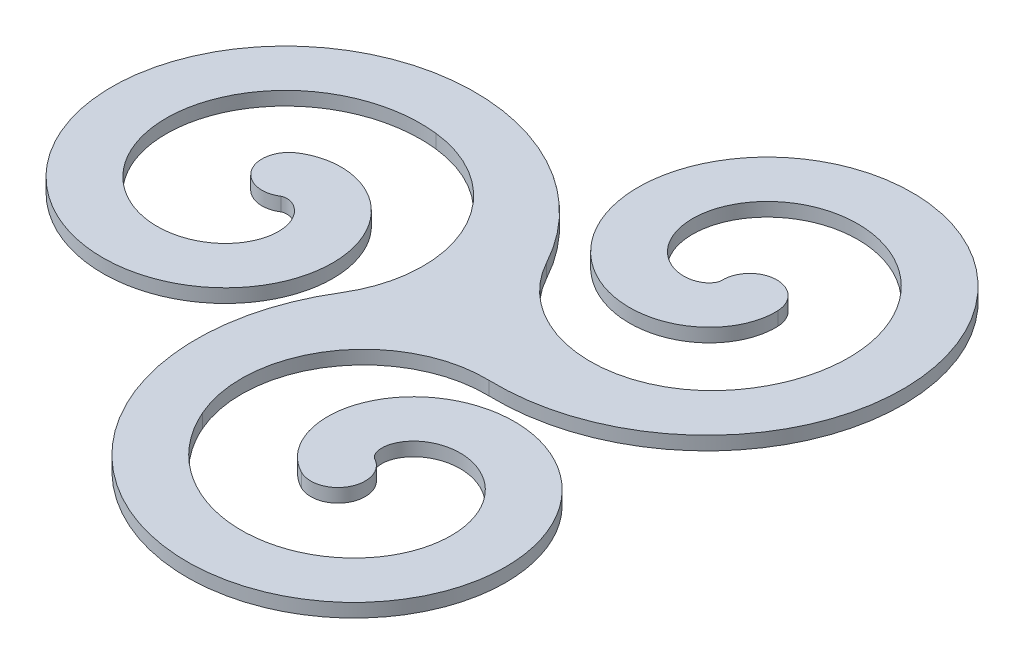
SolidWorks part; units mm, degrees
ref_plane "Ebene vorne" through (0, 0, 0) normal (0, 0, 1) x (1, 0, 0)
ref_plane "Ebene oben" through (0, 0, 0) normal (0, 1, 0) x (1, 0, 0)
ref_plane "Ebene rechts" through (0, 0, 0) normal (1, 0, 0) x (0, 0, -1)
sketch "Skizze1" plane through (0, 0, 0) normal (0, 1, 0) x (1, 0, 0)
  circle A0 centre (25, 0) radius 25
  dimension "D1" = 50
curve "Spirale/Helix1"
sketch "Skizze2" plane through (0, 0, 0) normal (0, 1, 0) x (1, 0, 0)
  arc A0 (35.7406, 8.1287) -> (14.2594, 41.8713) centre (25, 25) cw
  arc A1 (155.1116, -2.1102) -> (194.8884, 2.1102) centre (175, 0) ccw
  spline S0 degree 3 poles (908.2813, 493.7868) (28.4367, -157.1574) (-22.3322, 13.7047) (34.634, 28.7284) (37.4864, 29.0552) (43.449, 28.8209) (46.5585, 28.2594) (52.7591, 26.1542) (55.8493, 24.6101) (61.7076, 20.5299) (64.4748, 17.9937) (69.3815, 12.0105) (71.52, 8.5638) (74.8885, 0.9316) (76.1176, -3.2534) (77.4368, -12.1075) (77.5263, -16.776) (76.4101, -26.2759) (75.2039, -31.1064) (71.432, -40.5637) (68.8662, -45.1895) (62.4154, -53.8524) (58.5305, -57.8885) (49.5903, -64.9976) (44.5354, -68.0697) (33.5089, -72.9182) (27.5379, -74.6937) (15.0253, -76.6863) (8.4846, -76.9027) (-4.7487, -75.6097) (-11.4404, -74.0999) (-21.2435, -70.5012) (-24.4719, -69.0803) (-30.7904, -65.8009) (-33.8805, -63.9424) (-39.8631, -59.8013) (-42.7556, -57.5186) (-48.2845, -52.5502) (-50.9211, -49.8646) (-55.8824, -44.1198) (-58.2073, -41.0606) (-62.4928, -34.6056) (-64.4536, -31.2098) (-67.9632, -24.1258) (-69.512, -20.4376) (-72.1553, -12.8198) (-73.2498, -8.8903) (-74.9486, -0.8466) (-75.5529, 3.2674) (-76.2426, 11.6179) (-76.3279, 15.8543) (-75.959, 24.3831) (-75.5048, 28.6755) (-74.0445, 37.2467) (-73.0385, 41.5255) (-70.4717, 49.998) (-68.9109, 54.1916) (-65.2408, 62.4212) (-63.1315, 66.457) (-58.3802, 74.299) (-55.7383, 78.1049) (-49.9471, 85.4165) (-46.7978, 88.922) (-40.0268, 95.5648) (-36.4051, 98.7021) (-28.7328, 104.5448) (-24.6824, 107.2503) (-16.205, 112.1711) (-11.7781, 114.3864) (-2.6081, 118.2751) (2.135, 119.9485) (11.8702, 122.7089) (16.8622, 123.7959) (27.0217, 125.3478) (32.1892, 125.8126) (42.6214, 126.0935) (47.8859, 125.9096) (58.4299, 124.8764) (63.7093, 124.0271) (74.1979, 121.6571) (79.4072, 120.1364) (89.6696, 116.4285) (94.7227, 114.2412) (104.5868, 109.2162) (109.3979, 106.3784) (118.6938, 100.0793) (123.1785, 96.618) (131.7407, 89.11) (135.8181, 85.0633) (143.4889, 76.4329) (147.0822, 71.8494) (153.7142, 62.2041) (156.7527, 57.1423) (162.2116, 46.6087) (164.6319, 41.1367) (168.7991, 29.859) (170.546, 24.0533) (208.9501, -140.1066) (-9.8988, -387.3194) (-816.6254, 129.0757) knots -0.619464 -0.619464 -0.619464 -0.619464 0.03125 0.03125 0.0625 0.0625 0.09375 0.09375 0.125 0.125 0.15625 0.15625 0.1875 0.1875 0.21875 0.21875 0.25 0.25 0.28125 0.28125 0.3125 0.3125 0.34375 0.34375 0.375 0.375 0.40625 0.40625 0.4375 0.4375 0.46875 0.46875 0.484375 0.484375 0.5 0.5 0.515625 0.515625 0.53125 0.53125 0.546875 0.546875 0.5625 0.5625 0.578125 0.578125 0.59375 0.59375 0.609375 0.609375 0.625 0.625 0.640625 0.640625 0.65625 0.65625 0.671875 0.671875 0.6875 0.6875 0.703125 0.703125 0.71875 0.71875 0.734375 0.734375 0.75 0.75 0.765625 0.765625 0.78125 0.78125 0.796875 0.796875 0.8125 0.8125 0.828125 0.828125 0.84375 0.84375 0.859375 0.859375 0.875 0.875 0.890625 0.890625 0.90625 0.90625 0.921875 0.921875 0.9375 0.9375 0.953125 0.953125 0.96875 0.96875 0.984375 0.984375 1.401238 1.401238 1.401238 1.401238 only from (25, 25) to (175, 0) construction
  spline S1 degree 3 poles (25, 25) (27.0453, 26.3021) (29.4133, 27.3515) (34.634, 28.7284) (37.4864, 29.0552) (43.449, 28.8209) (46.5585, 28.2594) (52.7591, 26.1542) (55.8493, 24.6101) (61.7076, 20.5299) (64.4748, 17.9937) (69.3815, 12.0105) (71.52, 8.5638) (74.8885, 0.9316) (76.1176, -3.2534) (77.4368, -12.1075) (77.5263, -16.776) (76.4101, -26.2759) (75.2039, -31.1064) (71.432, -40.5637) (68.8662, -45.1895) (62.4154, -53.8524) (58.5305, -57.8885) (49.5903, -64.9976) (44.5354, -68.0697) (33.5089, -72.9182) (27.5379, -74.6937) (15.0253, -76.6863) (8.4846, -76.9027) (-4.7487, -75.6097) (-11.4404, -74.0999) (-21.2435, -70.5012) (-24.4719, -69.0803) (-30.7904, -65.8009) (-33.8805, -63.9424) (-39.8631, -59.8013) (-42.7556, -57.5186) (-48.2845, -52.5502) (-50.9211, -49.8646) (-55.8824, -44.1198) (-58.2073, -41.0606) (-62.4928, -34.6056) (-64.4536, -31.2098) (-67.9632, -24.1258) (-69.512, -20.4376) (-72.1553, -12.8198) (-73.2498, -8.8903) (-74.9486, -0.8466) (-75.5529, 3.2674) (-76.2426, 11.6179) (-76.3279, 15.8543) (-75.959, 24.3831) (-75.5048, 28.6755) (-74.0445, 37.2467) (-73.0385, 41.5255) (-70.4717, 49.998) (-68.9109, 54.1916) (-65.2408, 62.4212) (-63.1315, 66.457) (-58.3802, 74.299) (-55.7383, 78.1049) (-49.9471, 85.4165) (-46.7978, 88.922) (-40.0268, 95.5648) (-36.4051, 98.7021) (-28.7328, 104.5448) (-24.6824, 107.2503) (-16.205, 112.1711) (-11.7781, 114.3864) (-2.6081, 118.2751) (2.135, 119.9485) (11.8702, 122.7089) (16.8622, 123.7959) (27.0217, 125.3478) (32.1892, 125.8126) (42.6214, 126.0935) (47.8859, 125.9096) (58.4299, 124.8764) (63.7093, 124.0271) (74.1979, 121.6571) (79.4072, 120.1364) (89.6696, 116.4285) (94.7227, 114.2412) (104.5868, 109.2162) (109.3979, 106.3784) (118.6938, 100.0793) (123.1785, 96.618) (131.7407, 89.11) (135.8181, 85.0633) (143.4889, 76.4329) (147.0822, 71.8494) (153.7142, 62.2041) (156.7527, 57.1423) (162.2116, 46.6087) (164.6319, 41.1367) (168.7991, 29.859) (170.546, 24.0533) (173.321, 12.1917) (174.349, 6.1359) (175, 0) knots 0 0 0 0 0.03125 0.03125 0.0625 0.0625 0.09375 0.09375 0.125 0.125 0.15625 0.15625 0.1875 0.1875 0.21875 0.21875 0.25 0.25 0.28125 0.28125 0.3125 0.3125 0.34375 0.34375 0.375 0.375 0.40625 0.40625 0.4375 0.4375 0.46875 0.46875 0.484375 0.484375 0.5 0.5 0.515625 0.515625 0.53125 0.53125 0.546875 0.546875 0.5625 0.5625 0.578125 0.578125 0.59375 0.59375 0.609375 0.609375 0.625 0.625 0.640625 0.640625 0.65625 0.65625 0.671875 0.671875 0.6875 0.6875 0.703125 0.703125 0.71875 0.71875 0.734375 0.734375 0.75 0.75 0.765625 0.765625 0.78125 0.78125 0.796875 0.796875 0.8125 0.8125 0.828125 0.828125 0.84375 0.84375 0.859375 0.859375 0.875 0.875 0.890625 0.890625 0.90625 0.90625 0.921875 0.921875 0.9375 0.9375 0.953125 0.953125 0.96875 0.96875 0.984375 0.984375 1 1 1 1 construction
  spline S2 degree 1 poles (35.7406, 8.1287) (155.1116, -2.1102) knots 0 0 1 1 construction
  spline S3 degree 3 poles (35.7406, 8.1287) (35.8159, 8.1767) (35.9534, 8.2571) (36.381, 8.4663) (37.0711, 8.714) (38.216, 8.9346) (40.1146, 9.0131) (43.1288, 8.5114) (47.3461, 6.4526) (51.5749, 2.628) (55.1346, -3.0458) (57.3291, -10.4114) (57.5224, -19.0758) (55.2104, -28.4373) (50.0814, -37.7314) (42.0622, -46.0931) (31.3445, -52.6299) (18.3901, -56.5013) (3.9124, -56.9978) (-11.1634, -53.6132) (-25.7606, -46.1043) (-38.7271, -34.5327) (-48.9222, -19.2843) (-55.3072, -1.0649) (-57.0346, 19.1303) (-53.5273, 40.0705) (-44.5416, 60.365) (-30.2096, 78.5549) (-11.056, 93.2158) (12.0137, 103.0632) (37.7524, 107.0547) (64.6387, 104.4797) (90.9664, 95.0299) (114.9539, 78.8477) (131.5416, 60.2566) (141.9883, 42.8543) (148.2436, 28.7159) (152.0148, 16.1832) (154.1026, 5.827) (154.8309, 0.5361) (155.1116, -2.1102) knots 0 0 0 0 0.007812 0.015625 0.03125 0.046875 0.0625 0.09375 0.125 0.15625 0.1875 0.21875 0.25 0.28125 0.3125 0.34375 0.375 0.40625 0.4375 0.46875 0.5 0.53125 0.5625 0.59375 0.625 0.65625 0.6875 0.71875 0.75 0.78125 0.8125 0.84375 0.875 0.90625 0.9375 0.953125 0.96875 0.984375 0.992188 1 1 1 1
  spline S4 degree 1 poles (14.2594, 41.8713) (194.8884, 2.1102) knots 0 0 1 1 construction
  spline S5 degree 3 poles (14.2594, 41.8713) (16.1875, 43.0987) (20.2161, 45.2367) (29.0673, 48.3164) (41.1651, 49.6503) (56.2084, 46.885) (70.5337, 39.6797) (82.9101, 28.2868) (92.1834, 13.2795) (97.3649, -4.4658) (97.7098, -23.814) (92.7852, -43.4374) (82.5195, -61.9004) (67.2287, -77.7568) (47.6159, -89.6546) (24.7428, -96.4378) (-0.0256, -97.2409) (-25.1017, -91.5672) (-48.7752, -79.3445) (-69.3267, -60.9538) (-85.1478, -37.2273) (-94.8595, -9.415) (-97.4194, 20.8799) (-92.2115, 51.7929) (-79.1103, 81.3123) (-58.5143, 107.4088) (-31.3449, 128.1726) (0.9897, 141.9479) (36.6661, 147.4565) (73.5477, 143.9011) (109.3126, 131.0408) (141.6003, 109.2334) (163.7339, 84.4011) (177.5941, 61.306) (185.8607, 42.6156) (190.8248, 26.1122) (193.5664, 12.51) (194.5203, 5.5791) (194.8884, 2.1102) knots 0 0 0 0 0.015625 0.03125 0.0625 0.09375 0.125 0.15625 0.1875 0.21875 0.25 0.28125 0.3125 0.34375 0.375 0.40625 0.4375 0.46875 0.5 0.53125 0.5625 0.59375 0.625 0.65625 0.6875 0.71875 0.75 0.78125 0.8125 0.84375 0.875 0.90625 0.9375 0.953125 0.96875 0.984375 0.992188 1 1 1 1
  dimension "D1" = 20
  dimension "D2" = 20
extrude "Aufsatz-Linear austragen1" add sketch "Skizze2" along normal blind 10
ref_plane "Ebene1" through (175, 0, 0) normal (1, 0, 0) x (0, 0, -1)
ref_axis "Achse1" through (175, 10.5, 0) along (0, -1, 0)
pattern_circular "Kreismuster1" count 3 over 360 about axis through (175, 10.5, 0) along (0, -1, 0) of bodies 101
combine bodies "Kombinieren1" operation type add bodies to combine 101 102 103
fillet "Verrundung1" radius 90 3 edges at (193.1394, 5, -14.3218) (178.3333, 5, 22.87) (153.5273, 5, -8.5483)
